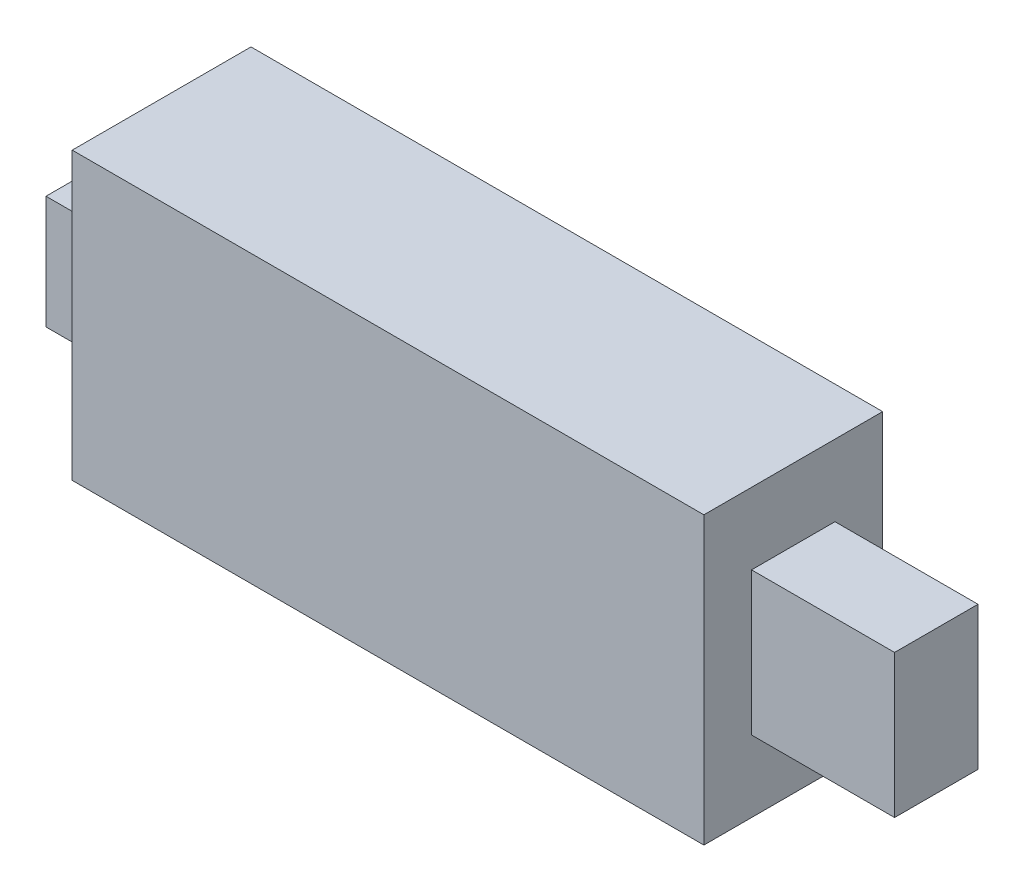
SolidWorks part; units mm, degrees
material "ABS"
ref_plane "前视基准面" through (0, 0, 0) normal (0, 0, 1) x (1, 0, 0)
ref_plane "上视基准面" through (0, 0, 0) normal (0, 1, 0) x (1, 0, 0)
ref_plane "右视基准面" through (0, 0, 0) normal (1, 0, 0) x (0, 0, -1)
other "Configuration Table"
sketch "草图1" plane through (0, 0, 0) normal (0, 0, 1) x (1, 0, 0)
  line L0 (-26.5, 0) -> (26.5, 0) construction
  line L1 (-26.5, 12) -> (26.5, 12)
  line L2 (-26.5, 12) -> (-26.5, -12)
  line L3 (-26.5, -12) -> (26.5, -12)
  line L4 (26.5, 12) -> (26.5, -12)
  point P6 (0, 0)
  dimension "D1" = 53
  dimension "D2" = 24
extrude "凸台-拉伸1" add sketch "草图1" along normal blind 15
sketch "草图2" plane through (26.5, 0, 0) normal (1, 0, 0) x (0, 0, -1)
  line L0 (-7.5, 12) -> (-7.5, -12) construction
  line L1 (-15, 12) -> (0, 12) construction
  line L2 (-15, -12) -> (0, -12) construction
  line L3 (-15, -12) -> (-15, 12) construction
  line L4 (-4, -6) -> (-11, -6)
  line L5 (-4, -6) -> (-4, 6)
  line L6 (-4, 6) -> (-11, 6)
  line L7 (-11, -6) -> (-11, 6)
  line L8 (-4, -6) -> (-11, 6) construction
  line L9 (-4, 6) -> (-11, -6) construction
  point P6 (-7.5, 0)
  dimension "D1" = 12
  dimension "D2" = 4
extrude "凸台-拉伸2" add sketch "草图2" along normal blind 12
sketch "草图3" plane through (-26.5, 0, 0) normal (-1, 0, 0) x (0, 0, 1)
  line L0 (7.5, 12) -> (7.5, -12) construction
  line L1 (15, 12) -> (0, 12) construction
  line L2 (15, -12) -> (0, -12) construction
  line L3 (0, 12) -> (0, -12) construction
  line L4 (12.2, -4.75) -> (2.8, -4.75)
  line L5 (12.2, -4.75) -> (12.2, 4.75)
  line L6 (12.2, 4.75) -> (2.8, 4.75)
  line L7 (2.8, -4.75) -> (2.8, 4.75)
  line L8 (12.2, -4.75) -> (2.8, 4.75) construction
  line L9 (12.2, 4.75) -> (2.8, -4.75) construction
  point P6 (7.5, 0)
  dimension "D1" = 9.5
  dimension "D2" = 2.8
extrude "凸台-拉伸3" add sketch "草图3" along normal blind 5
